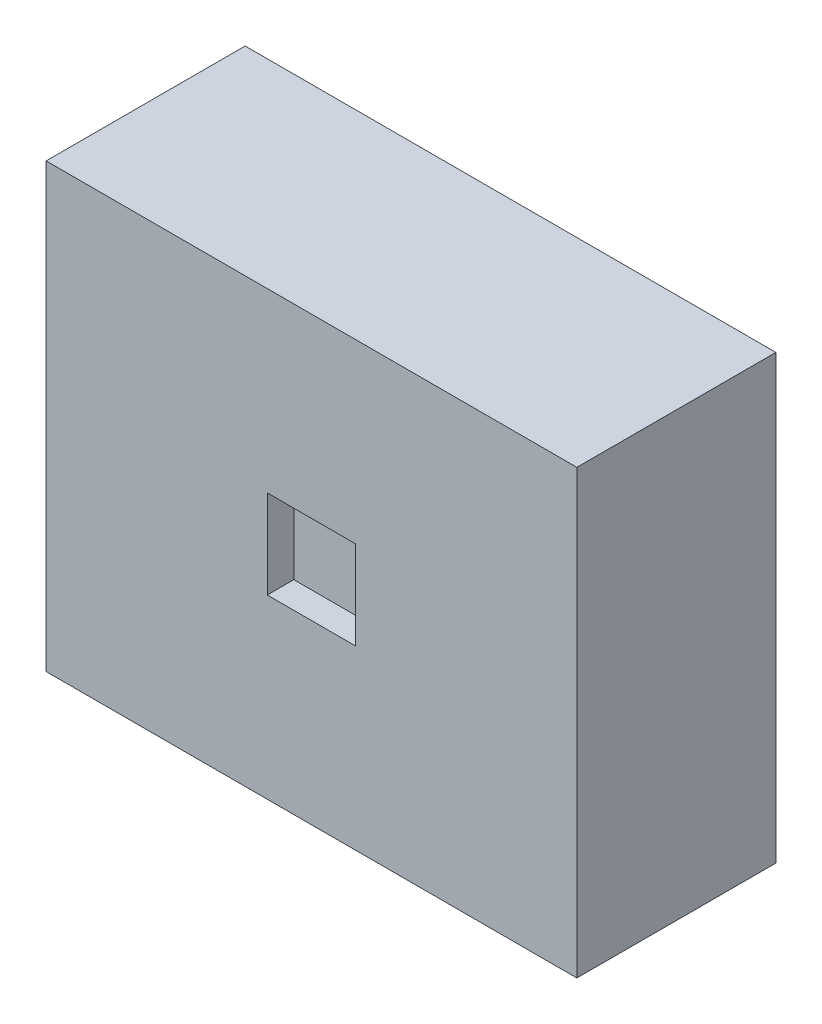
SolidWorks part; units mm, degrees
ref_plane "Front Plane" through (0, 0, 0) normal (0, 0, 1) x (1, 0, 0)
ref_plane "Top Plane" through (0, 0, 0) normal (0, 1, 0) x (1, 0, 0)
ref_plane "Right Plane" through (0, 0, 0) normal (1, 0, 0) x (0, 0, -1)
sketch "Sketch1" plane through (0, 0, 0) normal (0, 1, 0) x (1, 0, 0)
  line L1 (-60, -22.5) -> (60, -22.5)
  line L2 (-60, -22.5) -> (-60, 22.5)
  line L3 (-60, 22.5) -> (60, 22.5)
  line L4 (60, -22.5) -> (60, 22.5)
  line L5 (-60, -22.5) -> (60, 22.5) construction
  line L6 (-60, 22.5) -> (60, -22.5) construction
  point P0 (0, 0)
extrude "Boss-Extrude1" add sketch "Sketch1" along normal blind 100
sketch "Sketch3" plane through (0, 0, 22.5) normal (0, 0, 1) x (1, 0, 0)
  line L0 (-60, 100) -> (60, 0) construction
  line L1 (-60, 0) -> (60, 100) construction
  line L3 (-10, 40) -> (10, 40)
  line L4 (-10, 40) -> (-10, 60)
  line L5 (-10, 60) -> (10, 60)
  line L6 (10, 40) -> (10, 60)
  line L7 (-10, 40) -> (10, 60) construction
  line L8 (-10, 60) -> (10, 40) construction
  point P8 (0, 50)
extrude "Cut-Extrude2" cut sketch "Sketch3" against normal blind 6
sketch "Sketch4" plane through (0, 0, -22.5) normal (0, 0, -1) x (-1, 0, 0)
  line L0 (-60, 100) -> (60, 0) construction
  line L1 (-60, 0) -> (60, 100) construction
